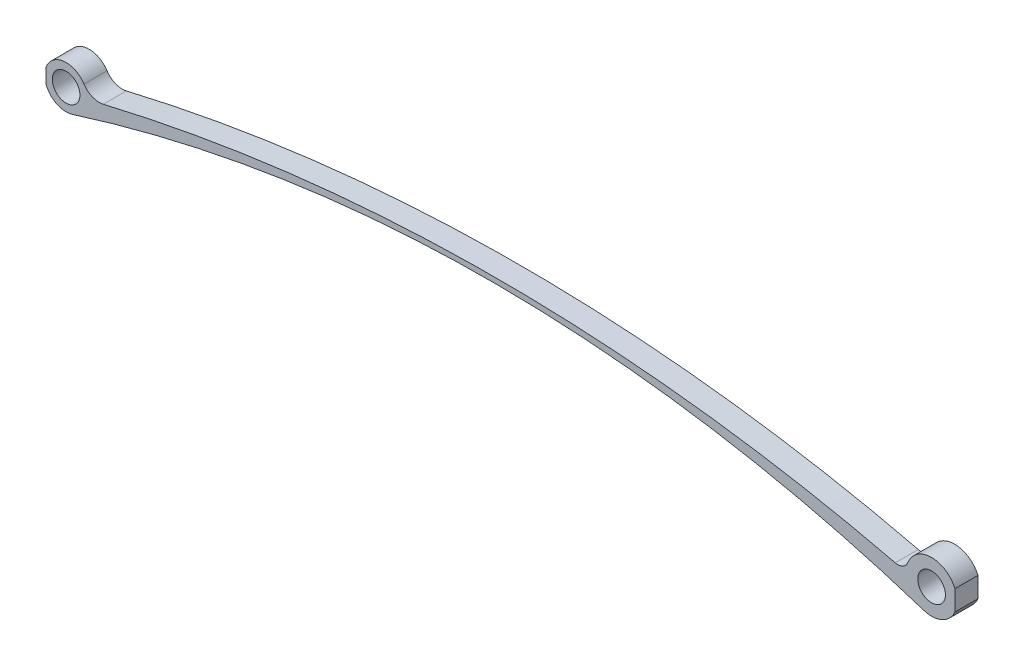
SolidWorks part; units mm, degrees
material "ABS"
ref_plane "Płaszczyzna przednia" through (0, 0, 0) normal (0, 0, 1) x (1, 0, 0)
ref_plane "Płaszczyzna górna" through (0, 0, 0) normal (0, 1, 0) x (1, 0, 0)
ref_plane "Płaszczyzna prawa" through (0, 0, 0) normal (1, 0, 0) x (0, 0, -1)
sketch "Szkic1" plane through (0, 0, 0) normal (0, 0, 1) x (1, 0, 0)
  line L0 (-3, 0) -> (187.7624, 0) construction
  line L1 (92.3812, 0) -> (92.3812, 21.7565) construction
  circle A0 centre (0, 0) radius 3
  circle A1 centre (187.7624, 0) radius 3
  arc A2 (186.0464, -5.2493) -> (182.6176, 2.0075) centre (187.7624, 0) ccw
  arc A3 (3.8882, 2.5232) -> (1.4006, -4.4185) centre (0, 0) ccw
  arc A4 (186.0464, -5.2493) -> (1.4006, -4.4185) centre (92.4333, -291.6097) ccw
  arc A5 (179.8775, 0.5757) -> (182.6176, 2.0075) centre (180.4268, 2.8623) ccw
  arc A6 (179.8775, 0.5757) -> (8.094, 0.8374) centre (93.4375, -359.2288) ccw
  arc A7 (3.8882, 2.5232) -> (8.094, 0.8374) centre (7.187, 4.6639) ccw
  point P10 (4.6352, 0)
  point P12 (182.2398, 0)
  dimension "D1" = 187.7624
  dimension "D2" = 6
  dimension "D3" = 5.5226
  dimension "D4" = 4.6352
  dimension "D6" = 2.3516
  dimension "D8" = 3.9325
extrude "Dodanie-wyciągnięcie1" add sketch "Szkic1" along normal blind 5
sketch "Szkic2" plane through (0, 0, 0) normal (0, 0, 1) x (1, 0, 0)
  line L0 (196.2931, 0) -> (-6.6873, 0) construction
  line L1 (192.8293, 4.1341) -> (192.8293, -3.3715)
  line L2 (-4.3568, -2.5646) -> (-4.3568, 2.4871)
  line L4 (-4.3568, 2.4871) -> (-5.0086, 2.4871)
  line L5 (-4.3568, 2.4871) -> (-4.3568, -2.5646)
  line L6 (-4.3568, -2.5646) -> (-5.0086, -2.5646)
  line L7 (-5.0086, 2.4871) -> (-5.0086, -2.5646)
  line L8 (192.8293, -3.3715) -> (194.4479, -3.3715)
  line L9 (192.8293, -3.3715) -> (192.8293, 4.1341)
  line L10 (192.8293, 4.1341) -> (194.4479, 4.1341)
  line L11 (194.4479, -3.3715) -> (194.4479, 4.1341)
extrude "Wytnij-wyciągnięcie3" cut sketch "Szkic2" along normal through all contours L0 L11 L10 L1 | L11 L0 L9 L8 | L0 L5 L4 L7 | L2 L0 L7 L6
